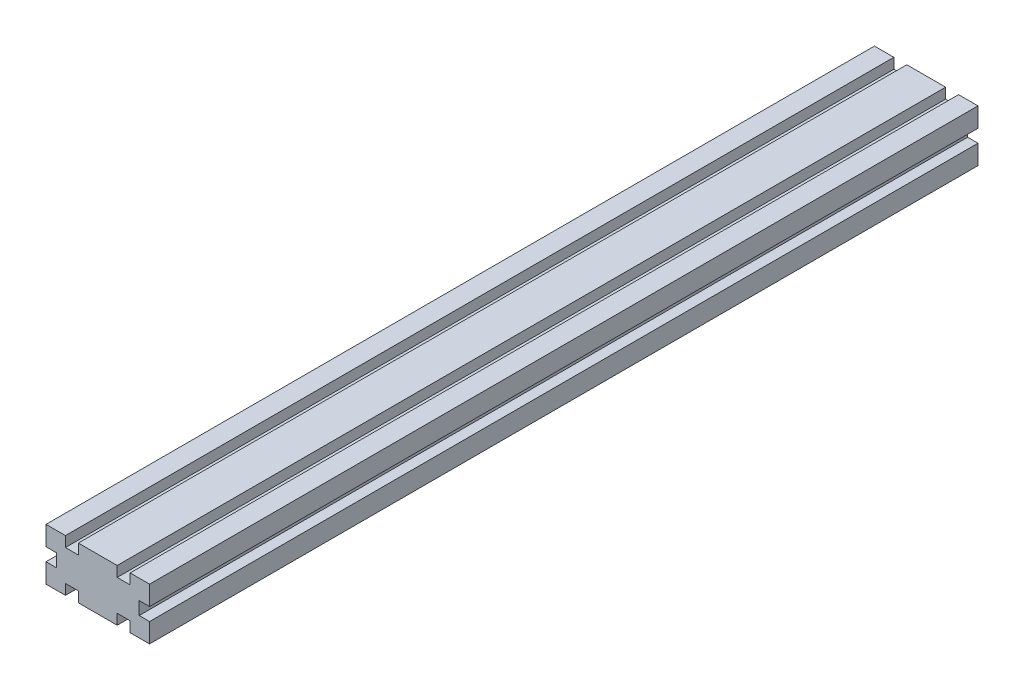
SolidWorks part; units mm, degrees
ref_plane "Plan de face" through (0, 0, 0) normal (0, 0, 1) x (1, 0, 0)
ref_plane "Plan de dessus" through (0, 0, 0) normal (0, 1, 0) x (1, 0, 0)
ref_plane "Plan de droite" through (0, 0, 0) normal (1, 0, 0) x (0, 0, -1)
sketch "Esquisse1" plane through (0, 0, 0) normal (0, 0, 1) x (1, 0, 0)
  line L0 (20, 20) -> (20, 0)
  line L1 (0, 0) -> (40, 0)
  line L2 (0, 0) -> (0, 20)
  line L3 (0, 20) -> (40, 20)
  line L4 (40, 0) -> (40, 20)
  line L5 (20, 0) -> (40, 20)
  line L6 (40, 0) -> (20, 20)
  line L7 (0, 0) -> (20, 20)
  line L8 (20, 0) -> (0, 20)
  line L10 (4, 4) -> (16, 4)
  line L11 (4, 4) -> (4, 16)
  line L12 (4, 16) -> (16, 16)
  line L13 (16, 4) -> (16, 16)
  line L14 (4, 4) -> (16, 16) construction
  line L15 (4, 16) -> (16, 4) construction
  line L16 (24, 4) -> (36, 4)
  line L17 (24, 4) -> (24, 16)
  line L18 (24, 16) -> (36, 16)
  line L19 (36, 4) -> (36, 16)
  line L20 (24, 4) -> (36, 16) construction
  line L21 (24, 16) -> (36, 4) construction
  line L22 (12.5, 0) -> (7.5, 0)
  line L23 (12.5, 0) -> (12.5, 20)
  line L24 (12.5, 20) -> (7.5, 20)
  line L25 (7.5, 0) -> (7.5, 20)
  line L26 (12.5, 0) -> (7.5, 20) construction
  line L27 (12.5, 20) -> (7.5, 0) construction
  line L28 (32.5, 0) -> (27.5, 0)
  line L29 (32.5, 0) -> (32.5, 20)
  line L30 (32.5, 20) -> (27.5, 20)
  line L31 (27.5, 0) -> (27.5, 20)
  line L32 (32.5, 0) -> (27.5, 20) construction
  line L33 (32.5, 20) -> (27.5, 0) construction
  line L34 (0, 7.5) -> (40, 7.5)
  line L35 (0, 7.5) -> (0, 12.5)
  line L36 (0, 12.5) -> (40, 12.5)
  line L37 (40, 7.5) -> (40, 12.5)
  line L38 (0, 7.5) -> (40, 12.5) construction
  line L39 (0, 12.5) -> (40, 7.5) construction
  point P7 (10, 10)
  point P12 (30, 10)
  point P17 (10, 10)
  point P22 (30, 10)
  point P27 (20, 10)
  dimension "D1" = 20
  dimension "D2" = 40
  dimension "D3" = 12
  dimension "D5" = 5
  dimension "D6" = 5
  dimension "D7" = 5
extrude "Boss.-Extru.1" add sketch "Esquisse1" along normal blind 320 contours L12 L25 L3 L8 | L2 L36 L11 L8 | L34 L2 L7 L11 | L1 L25 L10 L7 | L34 L11 L7 | L10 L25 L7 | L11 L36 L8 | L8 L25 L12 | L36 L11 L34 L25 | L25 L7 L8 | L36 L8 L7 | L8 L23 L7 | L7 L34 L8 | L23 L10 L8 | L34 L8 L13 | L34 L13 L8 L0 | L25 L36 L23 L12 | L36 L23 L34 L13 | L23 L7 L12 | L23 L12 L7 L3 | L7 L36 L13 | L13 L36 L0 L7 | L23 L1 L8 L10 | L34 L25 L10 L23 | L36 L13 L34 L0 | L36 L0 L34 L17 | L0 L36 L17 L6 | L18 L31 L3 L6 | L17 L36 L6 | L6 L31 L18 | L36 L17 L34 L31 | L34 L17 L5 | L34 L0 L5 L17 | L1 L31 L16 L5 | L16 L31 L5 | L34 L31 L16 L29 | L29 L16 L6 | L34 L6 L19 | L34 L19 L6 L4 | L29 L1 L6 L16 | L36 L29 L34 L19 | L6 L29 L5 | L5 L34 L6 | L31 L5 L6 | L36 L6 L5 | L5 L36 L19 | L29 L5 L18 | L29 L18 L5 L3 | L19 L36 L4 L5 | L31 L36 L29 L18
